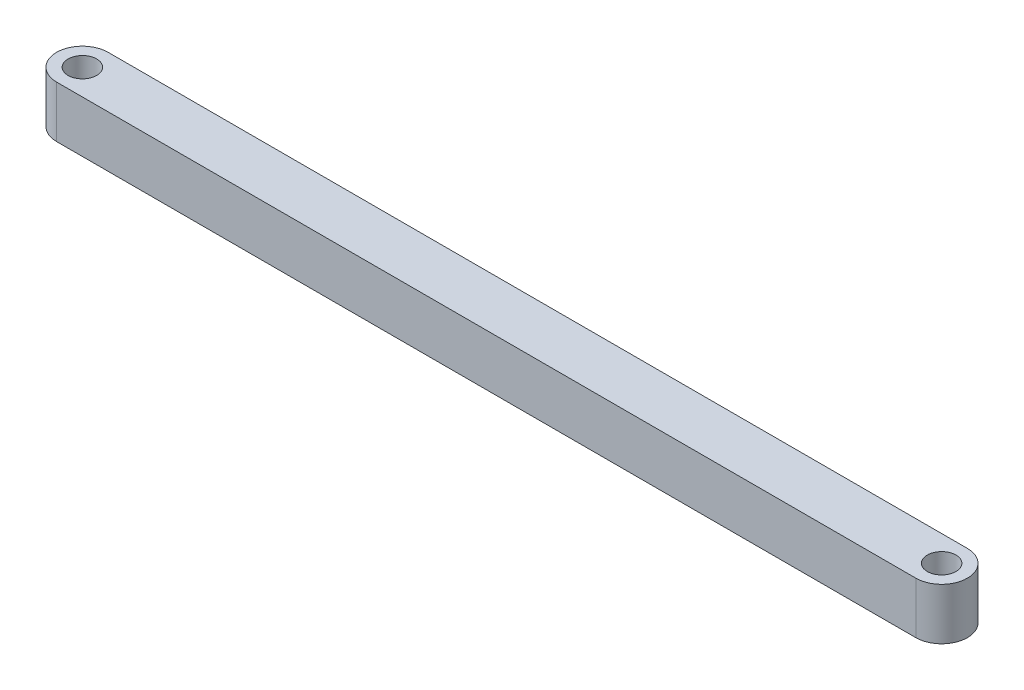
SolidWorks part; units mm, degrees
ref_plane "Front Plane" through (0, 0, 0) normal (0, 0, 1) x (1, 0, 0)
ref_plane "Top Plane" through (0, 0, 0) normal (0, 1, 0) x (1, 0, 0)
ref_plane "Right Plane" through (0, 0, 0) normal (1, 0, 0) x (0, 0, -1)
ref_plane "Plane1" through (0, 4.5, 0) normal (0, 1, 0) x (1, 0, 0)
sketch "Sketch1" plane through (0, 4.5, 0) normal (0, 1, 0) x (1, 0, 0)
  line L0 (75, 4.5) -> (-75, 4.5)
  line L1 (-75, -4.5) -> (75, -4.5)
  circle A0 centre (75, 0) radius 2.5
  arc A1 (-75, 4.5) -> (-75, -4.5) centre (-75, 0) ccw
  arc A2 (75, -4.5) -> (75, 4.5) centre (75, 0) ccw
  circle A3 centre (-75, 0) radius 2.5
  point P11 (0, 4.5)
  dimension "D1" = 4.5
  dimension "D2" = 5
  dimension "D3" = 150
extrude "Boss-Extrude1" add sketch "Sketch1" against normal blind 9
